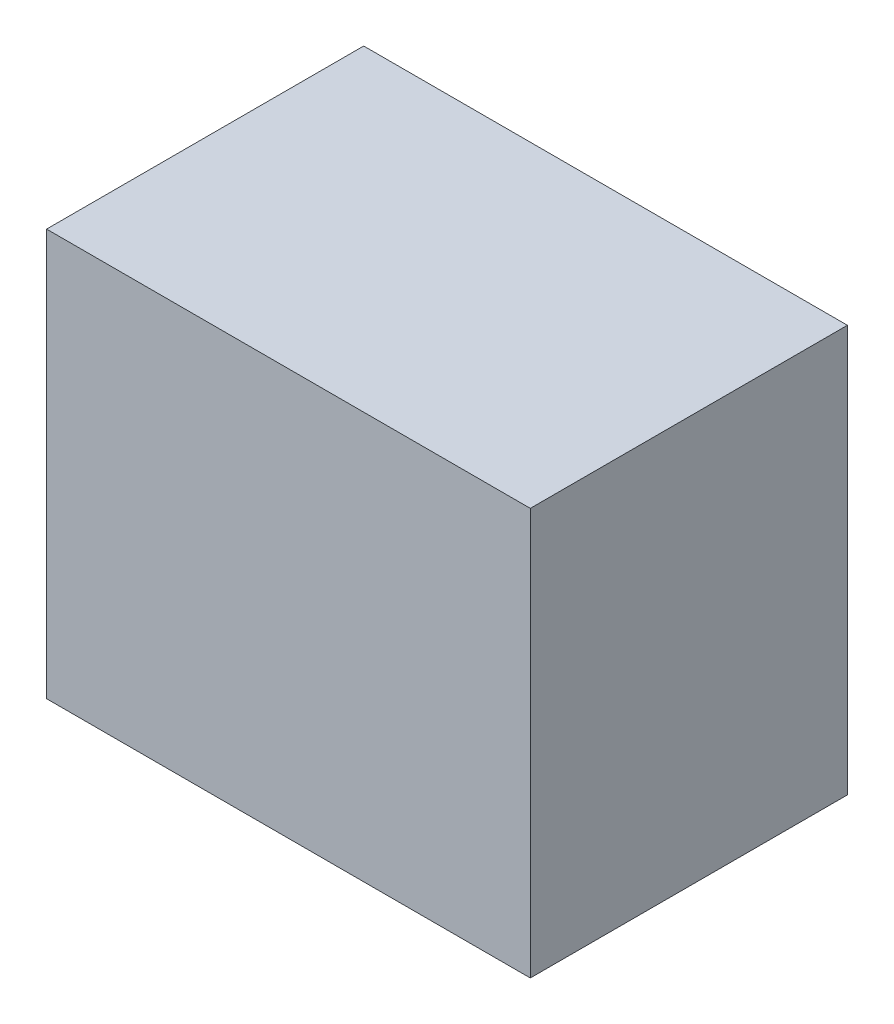
SolidWorks part; units mm, degrees
ref_plane "Front" through (0, 0, 0) normal (0, 0, 1) x (1, 0, 0)
ref_plane "Top" through (0, 0, 0) normal (0, 1, 0) x (1, 0, 0)
ref_plane "Right" through (0, 0, 0) normal (1, 0, 0) x (0, 0, -1)
sketch "Sketch1" plane through (0, 0, 0) normal (0, 1, 0) x (1, 0, 0)
  line L1 (0, 0) -> (106.934, 0)
  line L2 (0, 0) -> (0, 70.104)
  line L3 (0, 70.104) -> (106.934, 70.104)
  line L4 (106.934, 0) -> (106.934, 70.104)
  dimension "D1" = 106.934
  dimension "D2" = 70.104
extrude "Boss-Extrude1" add sketch "Sketch1" along normal blind 89.916
